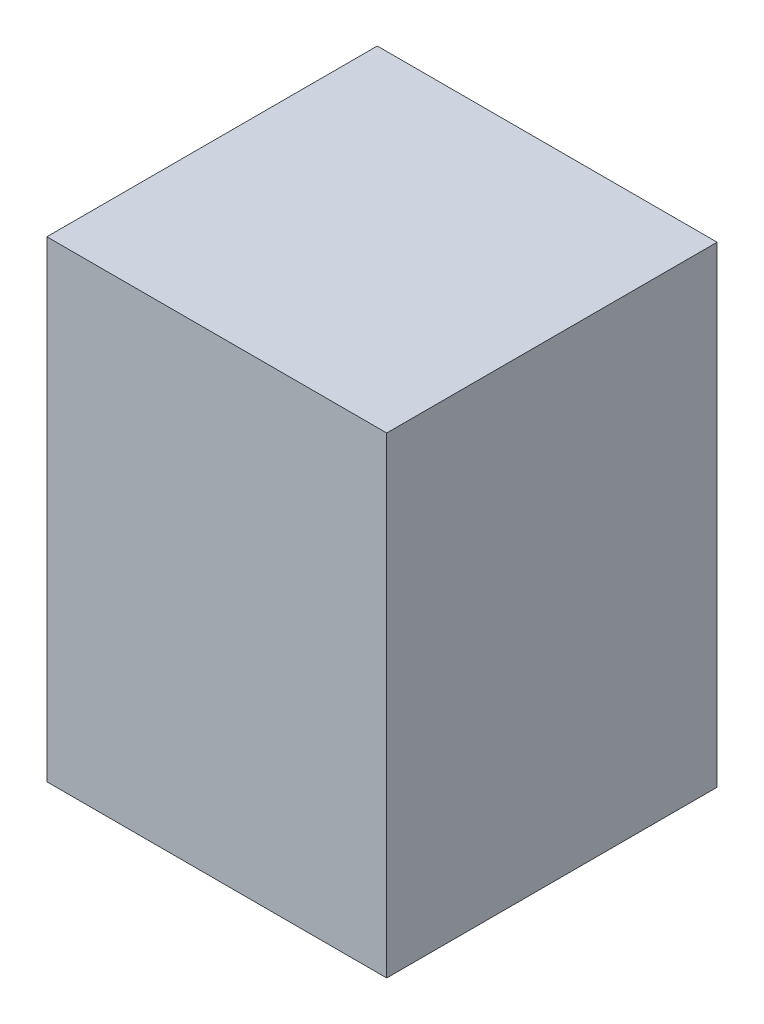
SolidWorks part; units mm, degrees
ref_plane "Front Plane" through (0, 0, 0) normal (0, 0, 1) x (1, 0, 0)
ref_plane "Top Plane" through (0, 0, 0) normal (0, 1, 0) x (1, 0, 0)
ref_plane "Right Plane" through (0, 0, 0) normal (1, 0, 0) x (0, 0, -1)
sketch "Sketch1" plane through (0, 0, 0) normal (0, 1, 0) x (1, 0, 0)
  line L0 (0, 0) -> (72, 0)
  line L1 (0, 0) -> (0, 70)
  line L2 (72, 0) -> (72, 70)
  line L3 (0, 70) -> (72, 70)
  dimension "D1" = 70
  dimension "D2" = 72
extrude "Boss-Extrude1" add sketch "Sketch1" along normal blind 100
sketch "Sketch2" plane through (0, 0, 0) normal (0, -1, 0) x (1, 0, 0)
  line L0 (40, 26.6473) -> (40, -123.3139) construction
  line L1 (0, -70) -> (0, 0) construction
  line L2 (72, -35) -> (0, -35) construction
  line L3 (72, 0) -> (72, -70) construction
  circle A0 centre (40, -5) radius 2.5
  dimension "D2" = 5
  dimension "D1" = 40
  dimension "D3" = 30
